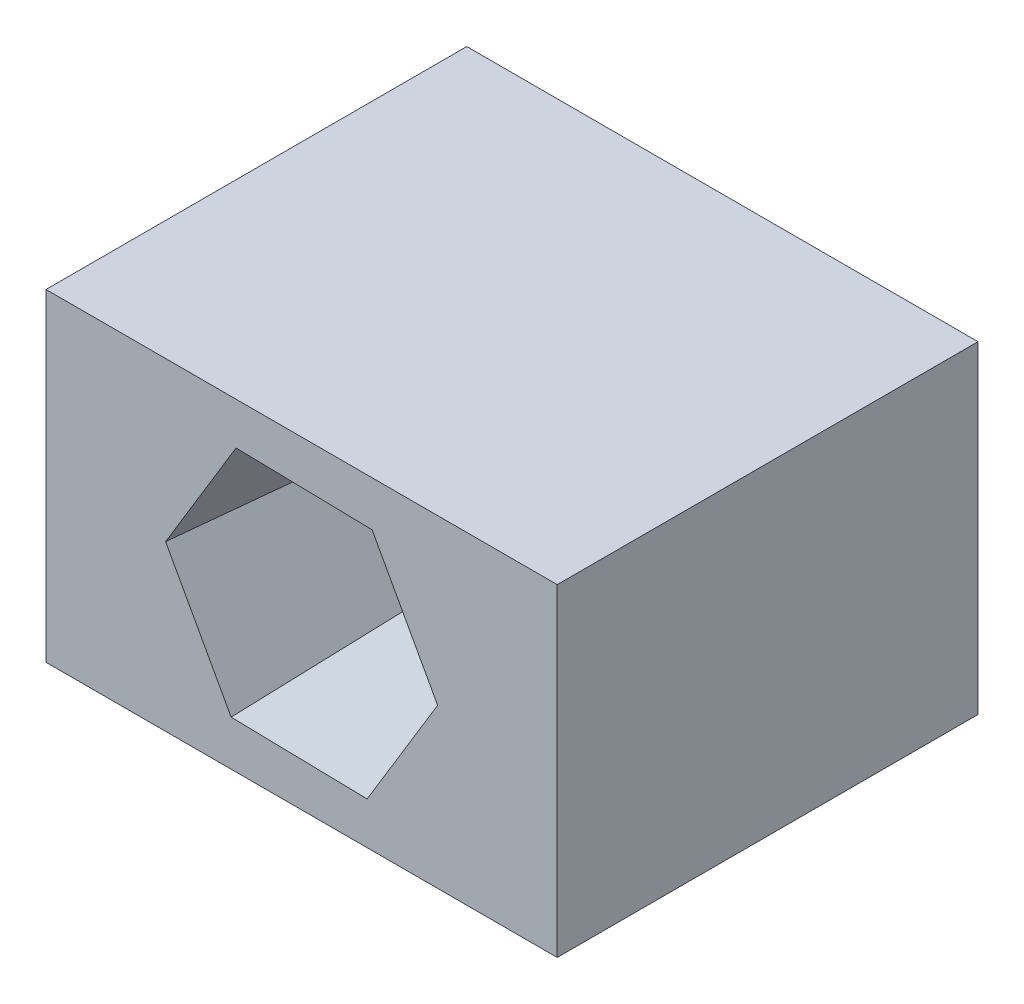
SolidWorks part; units mm, degrees
ref_plane "Plan de face" through (0, 0, 0) normal (0, 0, 1) x (1, 0, 0)
ref_plane "Plan de dessus" through (0, 0, 0) normal (0, 1, 0) x (1, 0, 0)
ref_plane "Plan de droite" through (0, 0, 0) normal (1, 0, 0) x (0, 0, -1)
sketch "Esquisse1" plane through (0, 0, 0) normal (0, 0, 1) x (1, 0, 0)
  line L1 (-6.0748, -3.8369) -> (6.0748, -3.8369)
  line L2 (-6.0748, -3.8369) -> (-6.0748, 3.8369)
  line L3 (-6.0748, 3.8369) -> (6.0748, 3.8369)
  line L4 (6.0748, -3.8369) -> (6.0748, 3.8369)
  line L5 (-6.0748, -3.8369) -> (6.0748, 3.8369) construction
  line L6 (-6.0748, 3.8369) -> (6.0748, -3.8369) construction
  circle A0 centre (0, 0) radius 1.7
  point P0 (0, 0)
extrude "Boss.-Extru.1" add sketch "Esquisse1" along normal blind 10
sketch "Esquisse2" plane through (0, 0, 10) normal (0, 0, 1) x (1, 0, 0)
  line L1 (1.6755, 2.7651) -> (-1.5569, 2.8336)
  line L2 (-1.5569, 2.8336) -> (-3.2324, 0.0685)
  line L3 (-3.2324, 0.0685) -> (-1.6755, -2.7651)
  line L4 (-1.6755, -2.7651) -> (1.5569, -2.8336)
  line L5 (1.5569, -2.8336) -> (3.2324, -0.0685)
  line L6 (3.2324, -0.0685) -> (1.6755, 2.7651)
  circle A0 centre (0, 0) radius 2.8 construction
extrude "Enlèv. mat.-Extru.1" cut sketch "Esquisse2" against normal blind 5 draft 5
